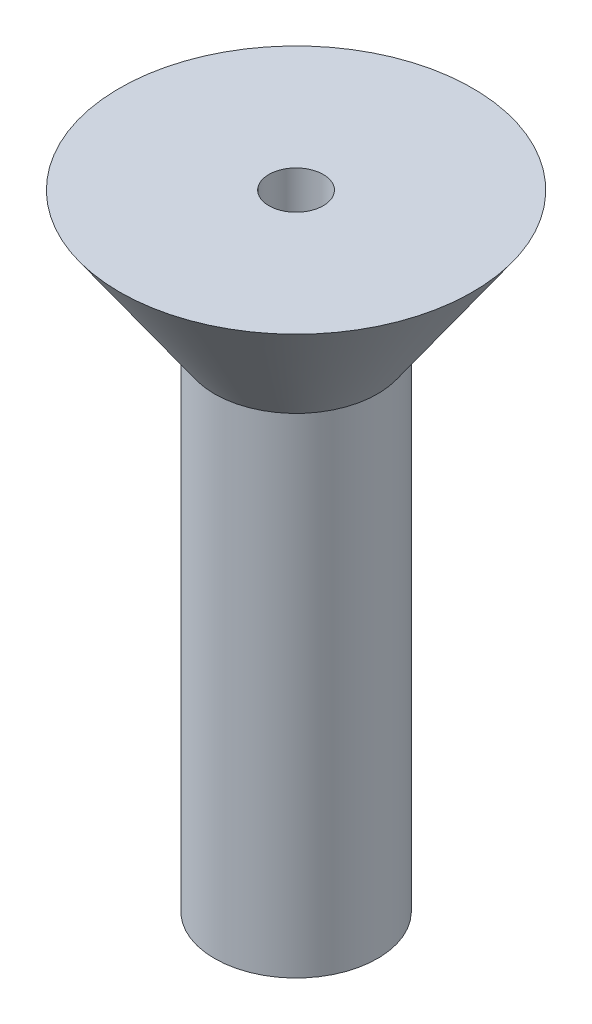
SolidWorks part; units mm, degrees
ref_plane "Front Plane" through (0, 0, 0) normal (0, 0, 1) x (1, 0, 0)
ref_plane "Top Plane" through (0, 0, 0) normal (0, 1, 0) x (1, 0, 0)
ref_plane "Right Plane" through (0, 0, 0) normal (1, 0, 0) x (0, 0, -1)
sketch "Sketch1" plane through (0, 0, 0) normal (0, 0, 1) x (1, 0, 0)
  line L0 (0, 91.9213) -> (0, -96.7487) construction
  line L1 (0, 0) -> (-3, 0)
  line L2 (-3, 0) -> (-3, 18)
  line L3 (-3, 18) -> (-6.5, 23)
  line L4 (-6.5, 23) -> (0, 23)
  line L5 (-3, 0) -> (0, -1.7321)
  line L6 (-3, 18) -> (0, 18)
  line L7 (-1, 23) -> (-1, 21)
  line L8 (-1, 21) -> (0, 21)
  line L9 (0, 23) -> (0, -1.7321)
  dimension "D1" = 18
  dimension "D2" = 3
  dimension "D3" = 60
  dimension "D4" = 5
  dimension "D5" = 6.5
  dimension "D6" = 1
  dimension "D7" = 2
revolve "Revolve3" add sketch "Sketch1" angle 360 about L0
